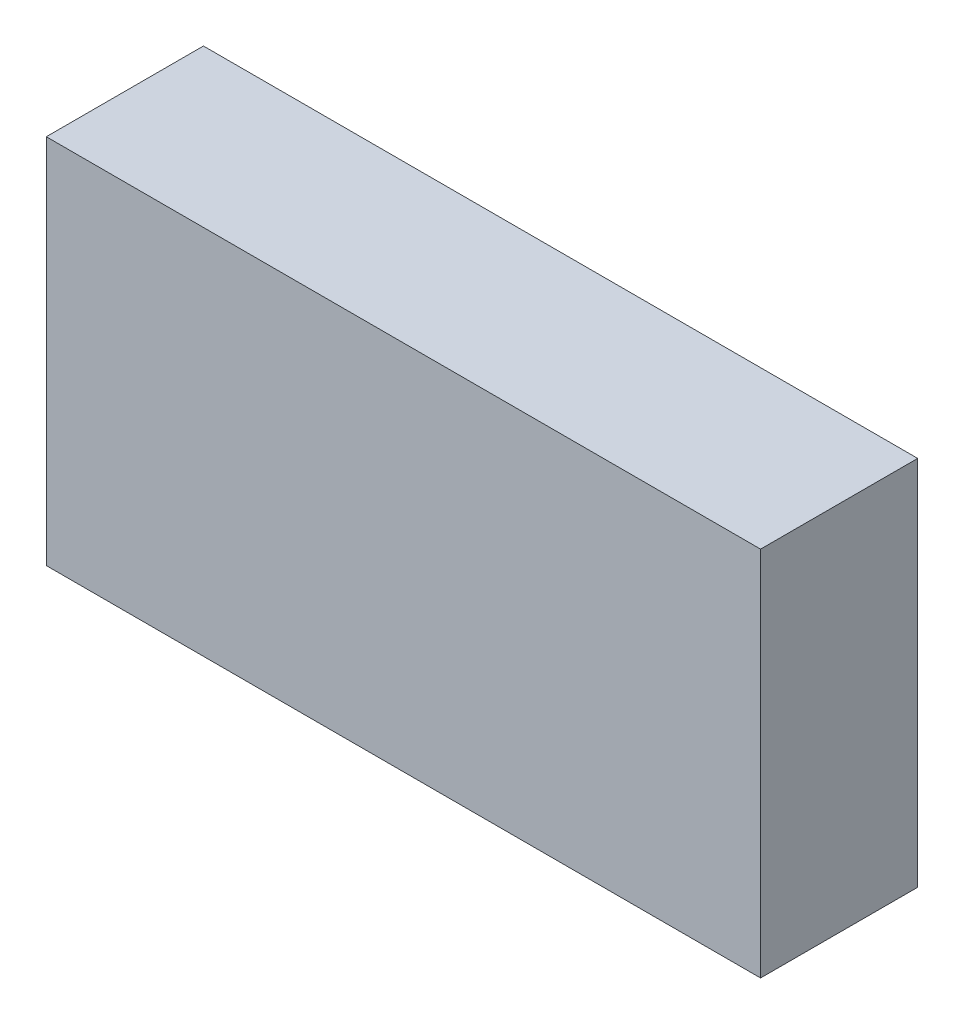
SolidWorks part; units mm, degrees
ref_plane "Спереди" through (0, 0, 0) normal (0, 0, 1) x (1, 0, 0)
ref_plane "Сверху" through (0, 0, 0) normal (0, 1, 0) x (1, 0, 0)
ref_plane "Справа" through (0, 0, 0) normal (1, 0, 0) x (0, 0, -1)
sketch "Эскиз1" plane through (0, 0, 0) normal (0, 0, 1) x (1, 0, 0)
  line L1 (36.5727, 66.6343) -> (-13.4273, 66.6343)
  line L2 (36.5727, 66.6343) -> (36.5727, 40.6343)
  line L3 (36.5727, 40.6343) -> (-13.4273, 40.6343)
  line L4 (-13.4273, 66.6343) -> (-13.4273, 40.6343)
  dimension "D1" = 26
  dimension "D2" = 50
extrude "Бобышка-Вытянуть1" add sketch "Эскиз1" along normal blind 11
